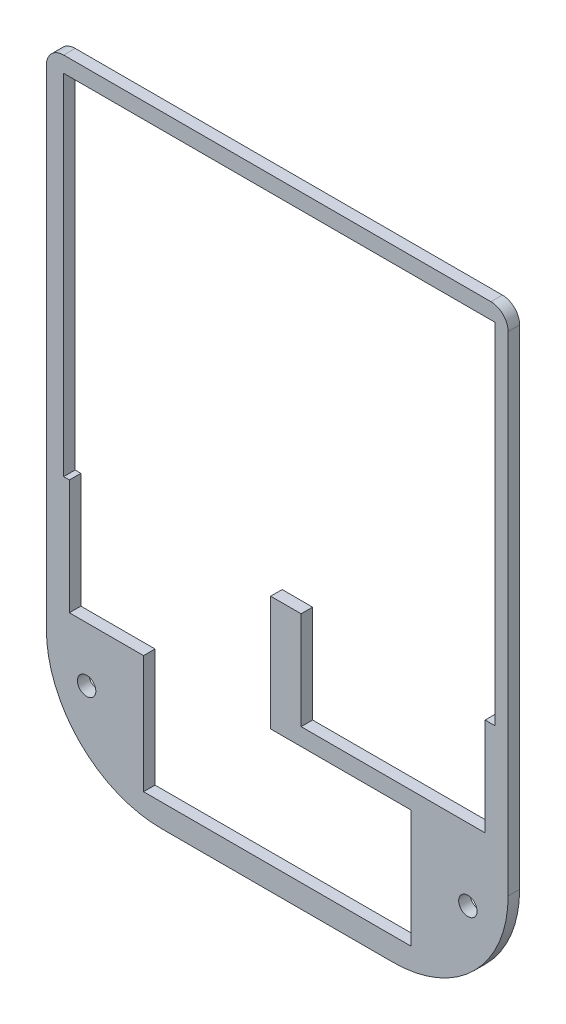
SolidWorks part; units mm, degrees
material "Acrylic (Medium-high impact)"
ref_plane "Front Plane" through (0, 0, 0) normal (0, 0, 1) x (1, 0, 0)
ref_plane "Top Plane" through (0, 0, 0) normal (0, 1, 0) x (1, 0, 0)
ref_plane "Right Plane" through (0, 0, 0) normal (1, 0, 0) x (0, 0, -1)
sketch "Sketch1" plane through (0, 0, 0) normal (0, 0, 1) x (1, 0, 0)
  line L1 (0, 0) -> (80.3, 0)
  line L2 (0, 0) -> (0, 66)
  line L3 (0, 66) -> (80.3, 66)
  line L4 (80.3, 0) -> (80.3, 66)
  dimension "D1" = 80.3
  dimension "D2" = 66
extrude "Boss-Extrude1" add sketch "Sketch1" along normal blind 2
hole_wizard "Ø3.2 (3.2) Diameter Hole1" positions "Sketch3" profile "Sketch2" hole size "Ø3.2" standard "ANSI Metric" end condition through all
sketch "Sketch3" plane through (0, 0, 2) normal (0, 0, 1) x (1, 0, 0)
  line L0 (0, 33) -> (80.3, 33) construction
  line L1 (0, 66) -> (0, 0) construction
  line L2 (80.3, 0) -> (80.3, 66) construction
  line L4 (7, 7) -> (7, 59) construction
  line L6 (7, 59) -> (73.3, 59) construction
  line L7 (73.3, 59) -> (73.3, 7) construction
  line L8 (73.3, 7) -> (7, 7) construction
  line L10 (40.15, 66) -> (40.15, 0) construction
  line L11 (80.3, 66) -> (0, 66) construction
  line L12 (0, 0) -> (80.3, 0) construction
  point P0 (7, 59)
  point P2 (73.3, 59)
  point P4 (73.3, 7)
  point P6 (7, 7)
  dimension "D1" = 66.3
  dimension "D2" = 52
  dimension "D3" = 26
  dimension "D4" = 33.15
sketch "Sketch2" plane through (7, 59, 2) normal (1, 0, 0) x (0, -1, 0)
  line L0 (0, 0) -> (0, 2)
  line L1 (0, 2) -> (1.6, 2)
  line L2 (1.6, 2) -> (1.6, 0)
  line L5 (1.6, 0) -> (0, 0)
  line L11 (0, -6.35) -> (0, 107.95) construction
  dimension "Thru Hole Dia." = 3.2
  dimension "Thru Hole Depth" = 2
fillet "Fillet1" radius 3 2 edges at (80.3, 66, 1) (0, 66, 1)
sketch "Sketch4" plane through (0, 0, 0) normal (0, -1, 0) x (1, 0, 0)
  line L4 (0, 0) -> (80.3, 0)
  line L5 (80.3, 0) -> (80.3, 2)
  line L6 (80.3, 2) -> (0, 2)
  line L7 (0, 2) -> (0, 0)
  line L8 (0, 0) -> (80.3, 0)
  line L9 (80.3, 0) -> (80.3, 2)
  line L10 (80.3, 2) -> (0, 2)
  line L11 (0, 2) -> (0, 0)
  dimension "D1" = 0
extrude "Boss-Extrude2" add sketch "Sketch4" along normal blind 42
fillet "Fillet2" radius 20 2 edges at (0, -42, 1) (80.3, -42, 1)
hole_wizard "Ø3.2 (3.2) Diameter Hole2" positions "Sketch6" profile "Sketch5" hole size "Ø3.2" standard "ANSI Metric"
sketch "Sketch6" plane through (0, 0, 2) normal (0, 0, 1) x (1, 0, 0)
  line L0 (7, -27) -> (73.3, -27) construction
  line L2 (40.15, -42) -> (40.15, 66) construction
  line L3 (60.3, -42) -> (20, -42) construction
  line L4 (77.3, 66) -> (3, 66) construction
  line L5 (40.15, -27) -> (40.15, -42) construction
  line L7 (0, 63) -> (0, -22) construction
  point P0 (7, -27)
  point P2 (73.3, -27)
  dimension "D1" = 15
  dimension "D2" = 7
sketch "Sketch5" plane through (7, -27, 2) normal (1, 0, 0) x (0, -1, 0)
  line L0 (0, 0) -> (0, 60.9614)
  line L1 (0, 60.9614) -> (1.6, 60)
  line L2 (1.6, 60) -> (1.6, 0)
  line L5 (1.6, 0) -> (0, 0)
  line L10 (0, 60.9614) -> (-1.6, 60) construction
  line L11 (0, -6.35) -> (0, 107.95) construction
  dimension "Hole Dia." = 3.2
  dimension "Hole Depth" = 60
  dimension "Drill Angle" = 118
sketch "Sketch7" plane through (0, 0, 2) normal (0, 0, 1) x (1, 0, 0)
  line L0 (3, 33) -> (78, 33) construction
  line L1 (3, 63.25) -> (78, 63.25)
  line L2 (3, 63.25) -> (3, 2.75)
  line L3 (3, 2.75) -> (78, 2.75)
  line L4 (78, 63.25) -> (78, 2.75)
  line L5 (7, 59) -> (7, 7) construction
  line L6 (7, 33) -> (80.3, 33) construction
  line L7 (80.3, -22) -> (80.3, 63) construction
  circle A0 centre (7, 59) radius 1.6 construction
  dimension "D1" = 75
  dimension "D2" = 60.5
  dimension "D3" = 4
extrude "Cut-Extrude1" cut sketch "Sketch7" against normal through all
sketch "Sketch10" plane through (0, 0, 2) normal (0, 0, 1) x (1, 0, 0)
  line L0 (76.3, -6) -> (44.3, -6) construction
  line L1 (4, 2.5) -> (39, 2.5)
  line L2 (4, 2.5) -> (4, -17.5)
  line L3 (4, -17.5) -> (39, -17.5)
  line L4 (39, 2.5) -> (39, -17.5)
  line L5 (44.3, 2.5) -> (76.3, 2.5)
  line L6 (44.3, 2.5) -> (44.3, -14.5)
  line L7 (44.3, -14.5) -> (76.3, -14.5)
  line L8 (76.3, 2.5) -> (76.3, -14.5)
  line L9 (16.9, -17.5) -> (63.4, -17.5)
  line L10 (16.9, -17.5) -> (16.9, -38)
  line L11 (16.9, -38) -> (63.4, -38)
  line L12 (63.4, -17.5) -> (63.4, -38)
  line L13 (39, -7.5) -> (4, -7.5) construction
  line L14 (40.15, -17.5) -> (40.15, -38) construction
  line L15 (40.15, -42) -> (40.15, 2.75) construction
  line L16 (60.3, -42) -> (20, -42) construction
  line L17 (3, 2.75) -> (78, 2.75) construction
  line L18 (0, 63) -> (0, -22) construction
  line L19 (80.3, -22) -> (80.3, 63) construction
  line L20 (77.3, 66) -> (3, 66) construction
  dimension "D1" = 32
  dimension "D2" = 17
  dimension "D3" = 35
  dimension "D4" = 20
  dimension "D5" = 20.5
  dimension "D6" = 46.5
  dimension "D7" = 63.5
  dimension "D8" = 4
  dimension "D9" = 4
extrude "Cut-Extrude3" cut sketch "Sketch10" against normal through all contours L4 L1 L2 L3 | L12 L9 L3 L10 L11 | L8 L5 L6 L7
sketch "Sketch11" plane through (0, 0, 2) normal (0, 0, 1) x (1, 0, 0)
  line L1 (3, 2.75) -> (78, 2.75)
  line L2 (3, 2.75) -> (3, 2.5)
  line L3 (3, 2.5) -> (78, 2.5)
  line L4 (78, 2.75) -> (78, 2.5)
extrude "Cut-Extrude4" cut sketch "Sketch11" against normal through all
